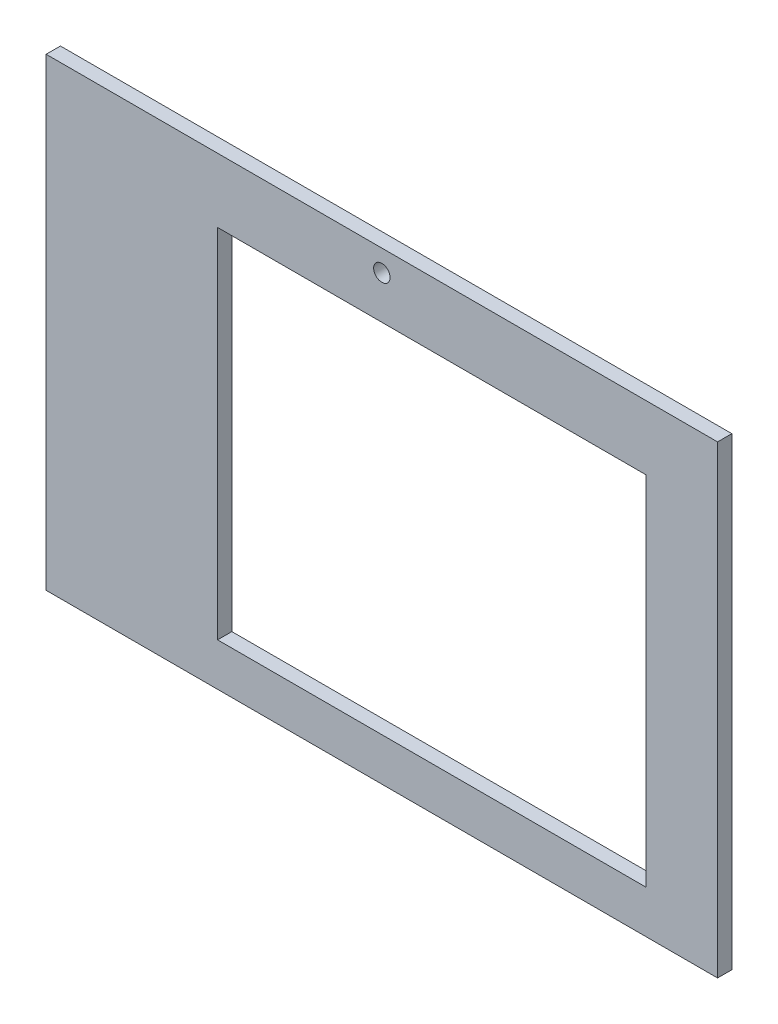
SolidWorks part; units mm, degrees
ref_plane "Front Plane" through (0, 0, 0) normal (0, 0, 1) x (1, 0, 0)
ref_plane "Top Plane" through (0, 0, 0) normal (0, 1, 0) x (1, 0, 0)
ref_plane "Right Plane" through (0, 0, 0) normal (1, 0, 0) x (0, 0, -1)
sketch "Croquis1" plane through (0, 0, 0) normal (0, 0, 1) x (1, 0, 0)
  line L0 (520.6747, 450) -> (524.2446, 178.6032) construction
  line L1 (-600, -475) -> (600, -475)
  line L2 (-600, -475) -> (-600, 475)
  line L3 (-600, 475) -> (600, 475)
  line L4 (600, -475) -> (600, 475)
  point P4 (600, 0)
  point P6 (0, -475)
  dimension "D1" = 950
  dimension "D2" = 1200
extrude "Saliente-Extruir1" add sketch "Croquis1" along normal blind 20
sketch "Croquis2" plane through (0, 0, 20) normal (0, 0, 1) x (1, 0, 0)
  line L1 (-275, 445) -> (-125, 445)
  line L2 (-275, 445) -> (-275, 265)
  line L3 (-275, 265) -> (-125, 265)
  line L4 (-125, 445) -> (-125, 265)
  line L5 (-600, 475) -> (-600, -475) construction
  line L6 (600, 475) -> (-600, 475) construction
  dimension "D1" = 150
  dimension "D2" = 180
  dimension "D3" = 30
  dimension "D4" = 325
extrude "Cortar-Extruir1" cut sketch "Croquis2" against normal blind 20
sketch "Croquis3" plane through (0, 0, 0) normal (0, 0, -1) x (-1, 0, 0)
  line L5 (-600, -475) -> (-600, 475) construction
  line L6 (600, -475) -> (-600, -475) construction
  line L7 (-420, -415) -> (180, -415)
  line L8 (-420, -415) -> (-420, 85)
  line L9 (-420, 85) -> (180, 85)
  line L10 (180, -415) -> (180, 85)
  dimension "D4" = 500
  dimension "D5" = 600
  dimension "D6" = 180
  dimension "D7" = 60
extrude "Cortar-Extruir2" cut sketch "Croquis3" against normal blind 20
sketch "Croquis5" plane through (0, 0, 0) normal (0, 0, -1) x (-1, 0, 0)
  line L0 (-600, -475) -> (-600, 475) construction
  line L1 (-600, 175) -> (600, 175)
  line L2 (-600, 175) -> (-600, 475)
  line L3 (-600, 475) -> (600, 475)
  line L4 (600, 175) -> (600, 475)
  line L5 (180, 85) -> (-420, 85) construction
  dimension "D1" = 90
extrude "Cortar-Extruir4" cut sketch "Croquis5" against normal blind 40
sketch "Croquis4" plane through (0, 0, 0) normal (0, 0, -1) x (-1, 0, 0)
  line L0 (-600, 175) -> (600, 175) construction
  line L1 (-600, -475) -> (-600, 175) construction
  circle A0 centre (-50, 145) radius 11.5
  dimension "D3" = 23
  dimension "D1" = 30
  dimension "D2" = 550
extrude "Cortar-Extruir5" cut sketch "Croquis4" against normal blind 40
sketch "Croquis6" plane through (0, 0, 0) normal (0, 0, -1) x (-1, 0, 0)
  line L0 (-600, 175) -> (600, 175) construction
  line L1 (-600, -475) -> (-520, -475)
  line L2 (-600, -475) -> (-600, 175)
  line L3 (-600, 175) -> (-520, 175)
  line L4 (-520, -475) -> (-520, 175)
  line L6 (600, -475) -> (422, -475)
  line L7 (600, -475) -> (600, 175)
  line L8 (600, 175) -> (422, 175)
  line L9 (422, -475) -> (422, 175)
  dimension "D1" = 80
  dimension "D2" = 178
extrude "Cortar-Extruir6" cut sketch "Croquis6" against normal blind 30
sketch "Croquis7" plane through (0, 0, 0) normal (0, 0, -1) x (-1, 0, 0)
  line L0 (-520, 175) -> (422, 175) construction
  line L1 (422, -475) -> (420, -475)
  line L2 (422, -475) -> (422, 175)
  line L3 (422, 175) -> (420, 175)
  line L4 (420, -475) -> (420, 175)
  dimension "D1" = 2
extrude "Cortar-Extruir7" cut sketch "Croquis7" against normal blind 30
